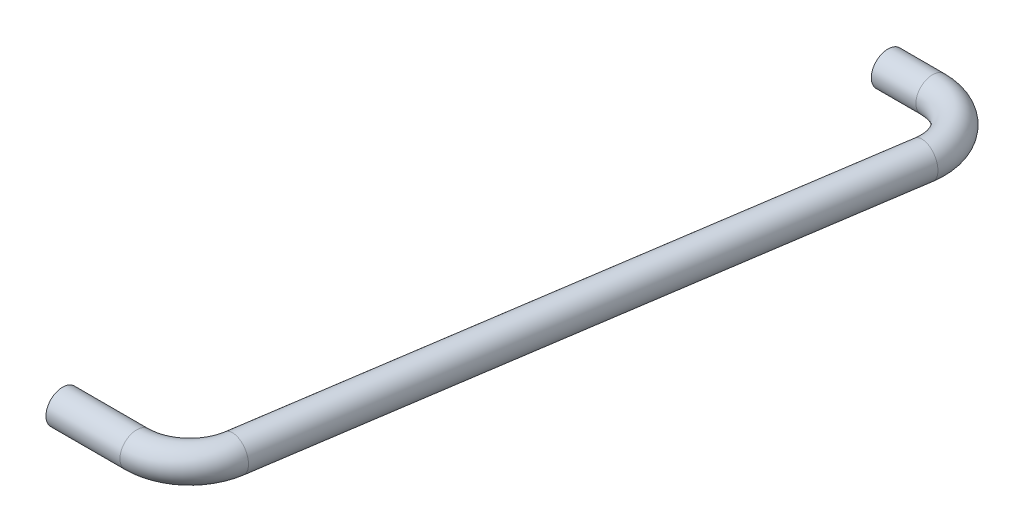
SolidWorks part; units mm, degrees
ref_plane "Front Plane" through (0, 0, 0) normal (0, 0, 1) x (1, 0, 0)
ref_plane "Top Plane" through (0, 0, 0) normal (0, 1, 0) x (1, 0, 0)
ref_plane "Right Plane" through (0, 0, 0) normal (1, 0, 0) x (0, 0, -1)
sketch "Sketch1" plane through (0, 0, 0) normal (0, 1, 0) x (1, 0, 0)
  line L0 (-4.6491, 0) -> (-8, 0)
  line L1 (-0.6939, -4.597) -> (-7.4863, -49.597)
  line L2 (-11.4415, -53) -> (-17, -53)
  arc A0 (-11.4415, -53) -> (-7.4863, -49.597) centre (-11.4415, -49) ccw
  arc A1 (-0.6939, -4.597) -> (-4.6491, 0) centre (-4.6491, -4) ccw
  point P7 (-8, -53)
  point P10 (0, 0)
  dimension "D3" = 4
  dimension "D1" = 9
  dimension "D2" = 8
  dimension "D4" = 53
ref_plane "Plane1" through (-8, 0, 0) normal (-1, 0, 0) x (0, 0, 1)
sketch "Sketch2" plane through (-8, 0, 0) normal (-1, 0, 0) x (0, 0, 1)
  circle A0 centre (0, 0) radius 1.25
  dimension "D1" = 2.5
sweep "Sweep1" add profiles "Sketch2" path "Sketch1"
